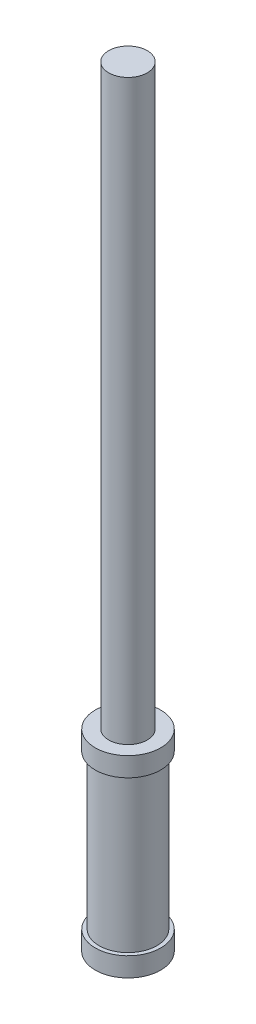
SolidWorks part; units mm, degrees
ref_plane "Front Plane" through (0, 0, 0) normal (0, 0, 1) x (1, 0, 0)
ref_plane "Top Plane" through (0, 0, 0) normal (0, 1, 0) x (1, 0, 0)
ref_plane "Right Plane" through (0, 0, 0) normal (1, 0, 0) x (0, 0, -1)
sketch "Sketch1" plane through (0, 0, 0) normal (0, 1, 0) x (1, 0, 0)
  circle A0 centre (0, 0) radius 8.5
extrude "Boss-Extrude1" add sketch "Sketch1" along normal blind 50
sketch "Sketch2" plane through (0, 50, 0) normal (0, 1, 0) x (1, 0, 0)
  circle A0 centre (0, 0) radius 5
extrude "Boss-Extrude2" add sketch "Sketch2" along normal blind 150
ref_plane "Plane1" through (0, 45, 0) normal (0, 1, 0) x (1, 0, 0)
sketch "Sketch3" plane through (0, 45, 0) normal (0, 1, 0) x (1, 0, 0)
  circle A0 centre (0, 0) radius 7.5
  circle A1 centre (0, 0) radius 8.5
extrude "Cut-Extrude1" cut sketch "Sketch3" against normal blind 40
